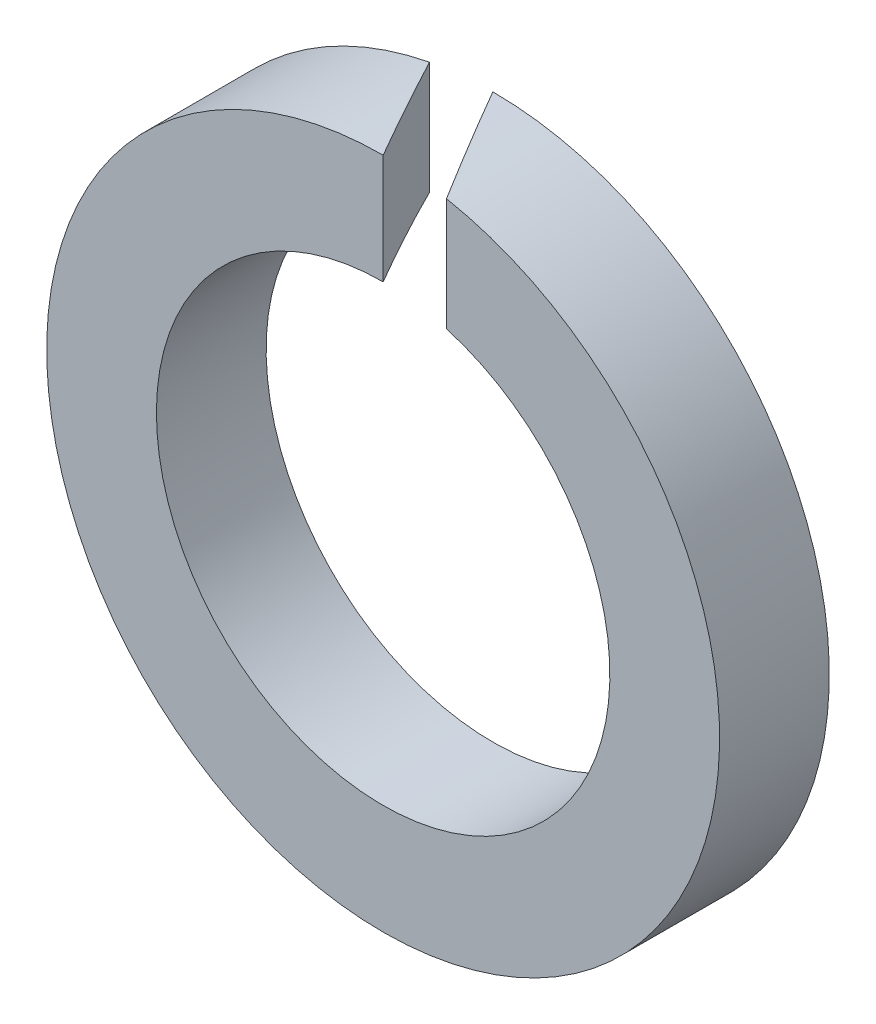
SolidWorks part; units mm, degrees
ref_plane "Front Plane" through (0, 0, 0) normal (0, 0, 1) x (1, 0, 0)
ref_plane "Top Plane" through (0, 0, 0) normal (0, 1, 0) x (1, 0, 0)
ref_plane "Right Plane" through (0, 0, 0) normal (1, 0, 0) x (0, 0, -1)
sketch "草图1" plane through (0, 0, 0) normal (0, 0, 1) x (1, 0, 0)
  circle A0 centre (0, 0) radius 4.34
  circle A1 centre (0, 0) radius 6.44
  dimension "D1" = 8.68
  dimension "D2" = 2.1
extrude "凸台-拉伸1" add sketch "草图1" along normal blind 2.1
sketch "草图2" plane through (0, 0, 0) normal (0, 1, 0) x (1, 0, 0)
  line L0 (0, 0) -> (1.2124, -2.1)
  line L1 (-6.44, -2.1) -> (6.44, -2.1) construction
  line L2 (1.2124, -2.1) -> (0, -2.1)
  line L3 (-4.34, -2.1) -> (4.34, -2.1) construction
  line L4 (0, -2.1) -> (-1.2124, 0)
  line L5 (4.34, 0) -> (-4.34, 0) construction
  line L6 (-1.2124, 0) -> (0, 0)
  line L7 (6.44, 0) -> (-6.44, 0) construction
  dimension "D1" = 1.05
  dimension "D2" = 60
extrude "切除-拉伸1" cut sketch "草图2" along normal through all
